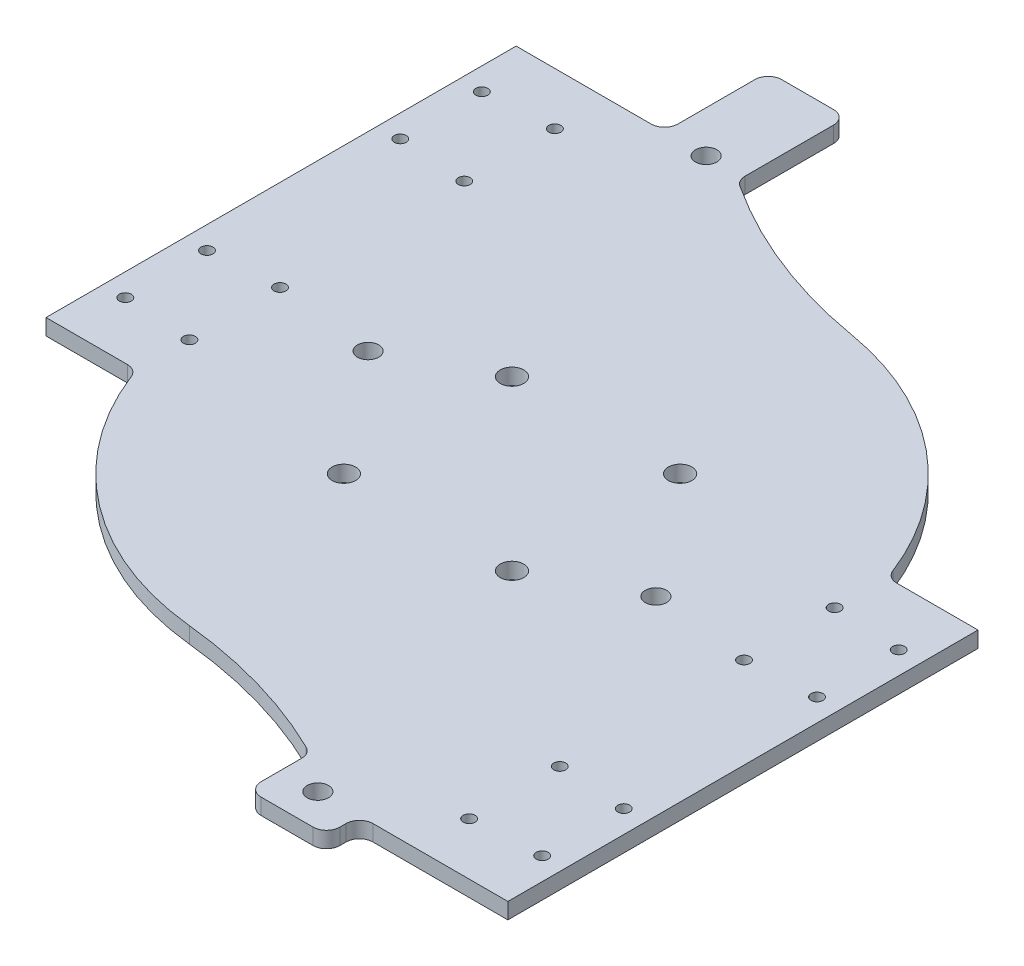
SolidWorks part; units mm, degrees
ref_plane "Front" through (0, 0, 0) normal (0, 0, 1) x (1, 0, 0)
ref_plane "Top" through (0, 0, 0) normal (0, 1, 0) x (1, 0, 0)
ref_plane "Right" through (0, 0, 0) normal (1, 0, 0) x (0, 0, -1)
sketch "Sketch1" plane through (0, 0, 0) normal (0, 1, 0) x (1, 0, 0)
  line L0 (-82.1382, -9.296) -> (-57.966, -9.296)
  line L5 (-38.0092, 157.3795) -> (-38.0092, 134.5189) construction
  line L6 (112.7675, 48.804) -> (136.9398, 48.804)
  line L7 (152.4008, 48.804) -> (112.7675, 48.804) construction
  line L8 (140.1148, 38.804) -> (140.1148, 0.704) construction
  line L9 (92.8108, -95.0108) -> (92.8108, -96.8298)
  line L10 (136.9398, 48.804) -> (136.9398, -91.0108)
  line L11 (96.8108, -91.0108) -> (152.4008, -91.0108) construction
  line L12 (136.9398, -91.0108) -> (96.8108, -91.0108)
  line L13 (88.8108, -100.8298) -> (73.4008, -100.8298)
  line L14 (69.4008, -96.8298) -> (69.4008, -84.8298)
  line L15 (-97.5992, -9.296) -> (-57.966, -9.296) construction
  line L16 (-82.1382, -9.296) -> (27.4008, -9.296) construction
  line L17 (27.4008, -9.296) -> (27.4008, 19.754) construction
  line L18 (27.4008, 19.754) -> (27.4008, 48.804) construction
  line L19 (27.4008, 48.804) -> (136.9398, 48.804) construction
  line L20 (-82.1382, -9.296) -> (-82.1382, 130.5189)
  line L21 (-42.0092, 130.5189) -> (-97.5992, 130.5189) construction
  line L22 (-82.1382, 130.5189) -> (-42.0092, 130.5189)
  line L23 (-38.0092, 134.5189) -> (-38.0092, 157.3795)
  line L24 (-34.0092, 161.3795) -> (-18.5951, 161.3795)
  line L25 (-14.5951, 157.3795) -> (-14.5951, 131.0601)
  arc A0 (-57.966, -9.296) -> (-54.2358, -11.8518) centre (-57.966, -13.296) cw
  arc A1 (-54.2358, -11.8518) -> (18.5083, -67.3343) centre (27.4008, 19.754) ccw
  arc A2 (18.5083, -67.3343) -> (67.2258, -81.2704) centre (3.8794, -210.5941) cw
  arc A3 (67.2258, -81.2704) -> (69.4008, -84.8298) centre (65.5171, -84.7587) cw
  arc A4 (69.4008, -96.8298) -> (73.4008, -100.8298) centre (73.4008, -96.8298) ccw
  arc A5 (88.8108, -100.8298) -> (92.8108, -96.8298) centre (88.8108, -96.8298) ccw
  arc A6 (92.8108, -95.0108) -> (96.8108, -91.0108) centre (96.8108, -95.0108) cw
  arc A7 (112.7675, 48.804) -> (109.0373, 51.3599) centre (112.7675, 52.804) cw
  arc A8 (109.0373, 51.3599) -> (42.1659, 106.041) centre (27.4008, 19.754) ccw
  arc A9 (42.1659, 106.041) -> (-12.4242, 127.5028) centre (66.4537, 247.978) cw
  arc A10 (-12.4242, 127.5028) -> (-14.5951, 131.0601) centre (-10.5951, 131.0601) cw
  arc A11 (-14.5951, 157.3795) -> (-18.5951, 161.3795) centre (-18.5951, 157.3795) ccw
  arc A12 (-34.0092, 161.3795) -> (-38.0092, 157.3795) centre (-34.0092, 157.3795) ccw
  arc A13 (-34.0092, 161.3795) -> (-38.0092, 157.3795) centre (-34.0092, 157.3795) ccw construction
  arc A14 (-38.0092, 134.5189) -> (-42.0092, 130.5189) centre (-42.0092, 134.5189) cw
  arc A15 (-12.4242, 127.5028) -> (42.1659, 106.041) centre (66.4537, 247.978) ccw construction
  arc A16 (-14.5951, 131.0601) -> (-12.4242, 127.5028) centre (-10.5951, 131.0601) ccw construction
  arc A17 (-14.5951, 157.3795) -> (-18.5951, 161.3795) centre (-18.5951, 157.3795) ccw construction
  arc A18 (-42.0092, 130.5189) -> (-38.0092, 134.5189) centre (-42.0092, 134.5189) ccw construction
  arc A19 (69.4008, -96.8298) -> (73.4008, -100.8298) centre (73.4008, -96.8298) ccw construction
  arc A20 (88.8108, -100.8298) -> (92.8108, -96.8298) centre (88.8108, -96.8298) ccw construction
  arc A21 (96.8108, -91.0108) -> (92.8108, -95.0108) centre (96.8108, -95.0108) ccw construction
  circle A22 centre (52.4008, 44.754) radius 3.5
  circle A23 centre (52.4008, -5.246) radius 3.5
  circle A24 centre (52.4008, -5.246) radius 3.5 construction
  circle A25 centre (52.4008, 44.754) radius 3.5 construction
  circle A26 centre (80.4008, 9.5509) radius 3.175
  circle A27 centre (80.4008, 9.5509) radius 3.175 construction
  circle A28 centre (109.8804, 33.2244) radius 1.778
  arc A29 (111.6584, 33.2244) -> (108.1024, 33.2244) centre (109.8804, 33.2244) ccw construction
  circle A30 centre (109.8804, 6.2837) radius 1.778
  arc A31 (108.1024, 6.2837) -> (111.6584, 6.2837) centre (109.8804, 6.2837) ccw construction
  circle A32 centre (109.8804, -48.5304) radius 1.778
  arc A33 (111.6584, -48.5304) -> (108.1024, -48.5304) centre (109.8804, -48.5304) ccw construction
  circle A34 centre (109.8804, -75.4712) radius 1.778
  arc A35 (111.6584, -75.4712) -> (108.1024, -75.4712) centre (109.8804, -75.4712) ccw construction
  circle A36 centre (130.2656, -49.8656) radius 1.778
  circle A37 centre (130.2656, -74.136) radius 1.778
  circle A38 centre (130.2656, 31.8893) radius 1.778
  circle A39 centre (130.2656, 7.6188) radius 1.778
  arc A40 (128.4876, 31.8893) -> (132.0436, 31.8893) centre (130.2656, 31.8893) ccw construction
  circle A41 centre (80.4008, -90.9853) radius 3.175
  circle A42 centre (2.4008, -5.246) radius 3.5
  circle A43 centre (2.4008, 44.754) radius 3.5
  circle A44 centre (-25.5992, 29.9572) radius 3.175
  circle A45 centre (-55.0788, 6.2837) radius 1.778
  circle A46 centre (-55.0788, 33.2244) radius 1.778
  circle A47 centre (-55.0788, 88.0385) radius 1.778
  circle A48 centre (-55.0788, 114.9793) radius 1.778
  circle A49 centre (-75.464, 89.3737) radius 1.778
  circle A50 centre (-75.464, 113.6441) radius 1.778
  circle A51 centre (-75.464, 7.6188) radius 1.778
  circle A52 centre (-75.464, 31.8893) radius 1.778
  circle A53 centre (-25.5992, 130.4934) radius 3.175
  circle A54 centre (2.4008, -5.246) radius 3.5 construction
  point P91 (27.4008, 19.754)
  point P162 (-11.8682, -26.0997)
  point P163 (27.4008, 19.754)
  point P188 (27.4008, 19.754)
  point P190 (-4.088, 3.6775)
  dimension "D1" = 3.175
  dimension "D2" = 2
extrude "Boss-Extrude1" add sketch "Sketch1" along normal blind 4.7625
